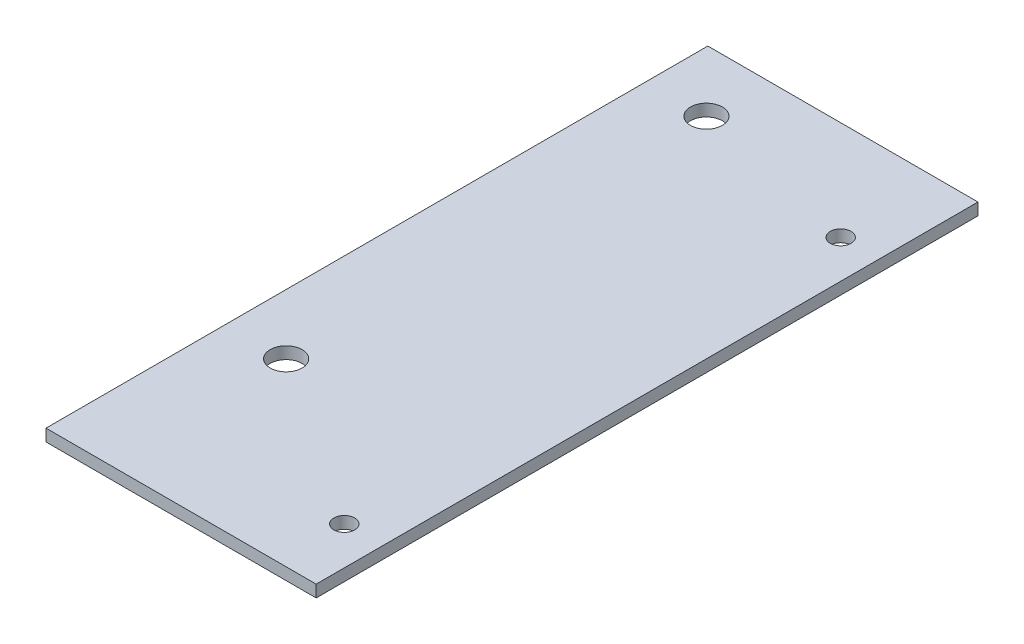
SolidWorks part; units mm, degrees
ref_plane "Front Plane" through (0, 0, 0) normal (0, 0, 1) x (1, 0, 0)
ref_plane "Top Plane" through (0, 0, 0) normal (0, 1, 0) x (1, 0, 0)
ref_plane "Right Plane" through (0, 0, 0) normal (1, 0, 0) x (0, 0, -1)
sketch "Sketch1" plane through (0, 0, 0) normal (0, 1, 0) x (1, 0, 0)
  line L1 (0, 0) -> (57.15, 0)
  line L2 (0, 0) -> (0, 140)
  line L3 (0, 140) -> (57.15, 140)
  line L4 (57.15, 0) -> (57.15, 140)
  dimension "D1" = 57.15
  dimension "D2" = 140
extrude "Boss-Extrude1" add sketch "Sketch1" along normal blind 2.54
sketch "Sketch2" plane through (0, 0, 0) normal (0, -1, 0) x (1, 0, 0)
  circle A0 centre (49.1, -119) radius 2.2
  circle A1 centre (49.1, -14) radius 2.2
  dimension "D1" = 4.4
  dimension "D2" = 4.4
extrude "Cut-Extrude1" cut sketch "Sketch2" against normal through all
sketch "Sketch3" plane through (0, 0, 0) normal (0, -1, 0) x (1, 0, 0)
  circle A0 centre (12.7, -127) radius 3.3782
  circle A1 centre (12.7, -38.1) radius 3.3782
  dimension "D1" = 6.7564
  dimension "D2" = 6.7564
extrude "Cut-Extrude2" cut sketch "Sketch3" against normal through all and the other way through all
